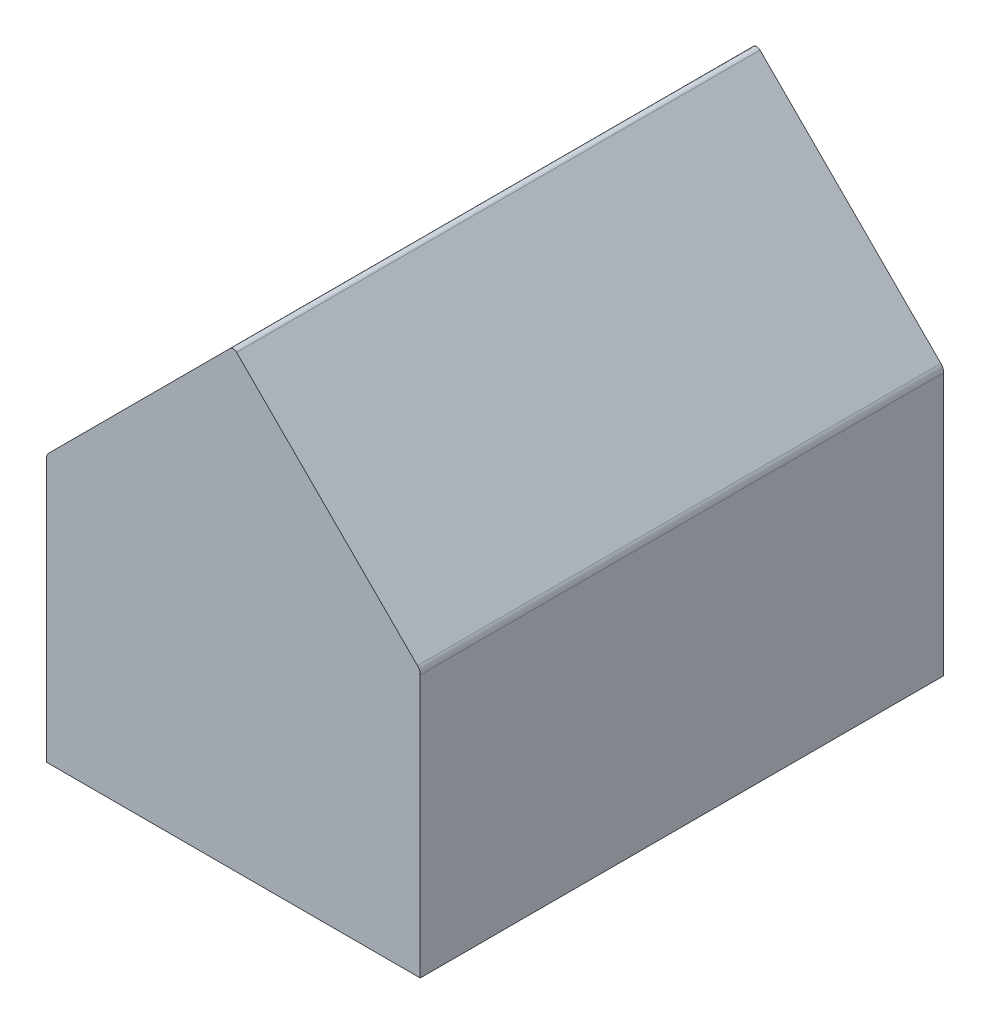
SolidWorks part; units mm, degrees
ref_plane "Front Plane" through (0, 0, 0) normal (0, 0, 1) x (1, 0, 0)
ref_plane "Top Plane" through (0, 0, 0) normal (0, 1, 0) x (1, 0, 0)
ref_plane "Right Plane" through (0, 0, 0) normal (1, 0, 0) x (0, 0, -1)
sketch "Sketch1" plane through (0, 0, 0) normal (0, 0, 1) x (1, 0, 0)
  line L0 (-5.08, 3.6195) -> (0, 8.6995)
  line L1 (-5.08, 3.6195) -> (5.08, 3.6195)
  line L2 (-5.08, 3.6195) -> (-5.08, -3.6195)
  line L3 (-5.08, -3.6195) -> (5.08, -3.6195)
  line L4 (5.08, 3.6195) -> (5.08, -3.6195)
  line L5 (-5.08, 3.6195) -> (5.08, -3.6195) construction
  line L6 (-5.08, -3.6195) -> (5.08, 3.6195) construction
  line L7 (0, 8.6995) -> (5.08, 3.6195)
  point P0 (0, 0)
  point P6 (0, 0)
  point P8 (0, 3.6195)
  dimension "D1" = 10.16
  dimension "D2" = 12.319
  dimension "D3" = 45
extrude "Boss-Extrude1" add sketch "Sketch1" along normal mid plane 14.224 contours L7 L0 L1 | L4 L1 L2 L3
fillet "Fillet2" radius 0.254 2 edges at (5.08, 3.6195, 0) (-5.08, 3.6195, 0)
fillet "Fillet3" radius 0.127 1 edges at (0, 8.6995, 0)
